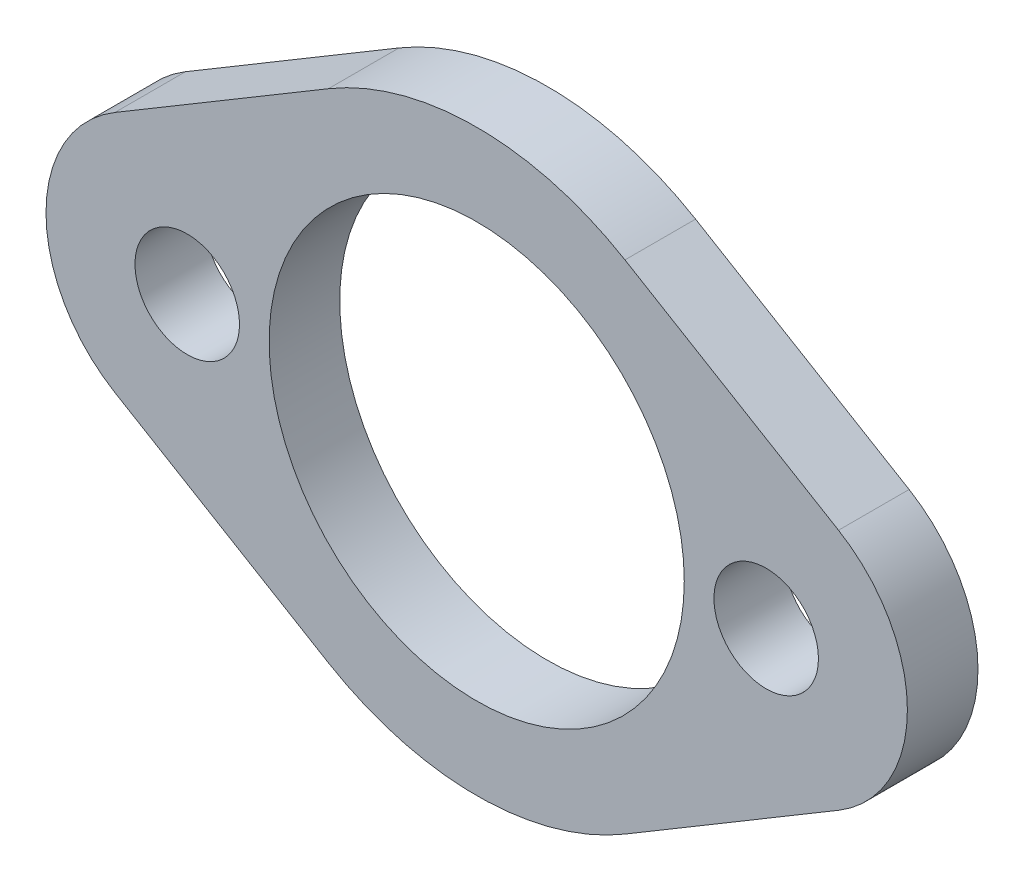
SolidWorks part; units mm, degrees
ref_plane "Front Plane" through (0, 0, 0) normal (0, 0, 1) x (1, 0, 0)
ref_plane "Top Plane" through (0, 0, 0) normal (0, 1, 0) x (1, 0, 0)
ref_plane "Right Plane" through (0, 0, 0) normal (1, 0, 0) x (0, 0, -1)
sketch "Sketch1" plane through (0, 0, 0) normal (0, 0, 1) x (1, 0, 0)
  line L0 (0, 38.6646) -> (0, -44.6392) construction
  line L1 (13.335, 22.3607) -> (32.5399, 10.9076)
  line L2 (-11.4695, 0) -> (11.2855, 0) construction
  line L3 (13.335, -22.3607) -> (32.5399, -10.9076)
  line L4 (-13.335, -22.3607) -> (-32.5399, -10.9076)
  line L5 (-13.335, 22.3607) -> (-32.5399, 10.9076)
  circle A0 centre (0, 0) radius 18.669
  arc A1 (13.335, 22.3607) -> (-13.335, 22.3607) centre (0, 0) ccw
  arc A2 (32.5399, -10.9076) -> (32.5399, 10.9076) centre (26.035, 0) ccw
  arc A3 (-32.5399, -10.9076) -> (-32.5399, 10.9076) centre (-26.035, 0) cw
  circle A4 centre (26.035, 0) radius 4.699
  circle A5 centre (-26.035, 0) radius 4.699
  arc A7 (-13.335, -22.3607) -> (13.335, -22.3607) centre (0, 0) ccw
  dimension "D1" = 37.338
  dimension "D2" = 52.07
  dimension "D3" = 25.4
  dimension "D4" = 9.398
extrude "Boss-Extrude1" add sketch "Sketch1" along normal blind 6.35
